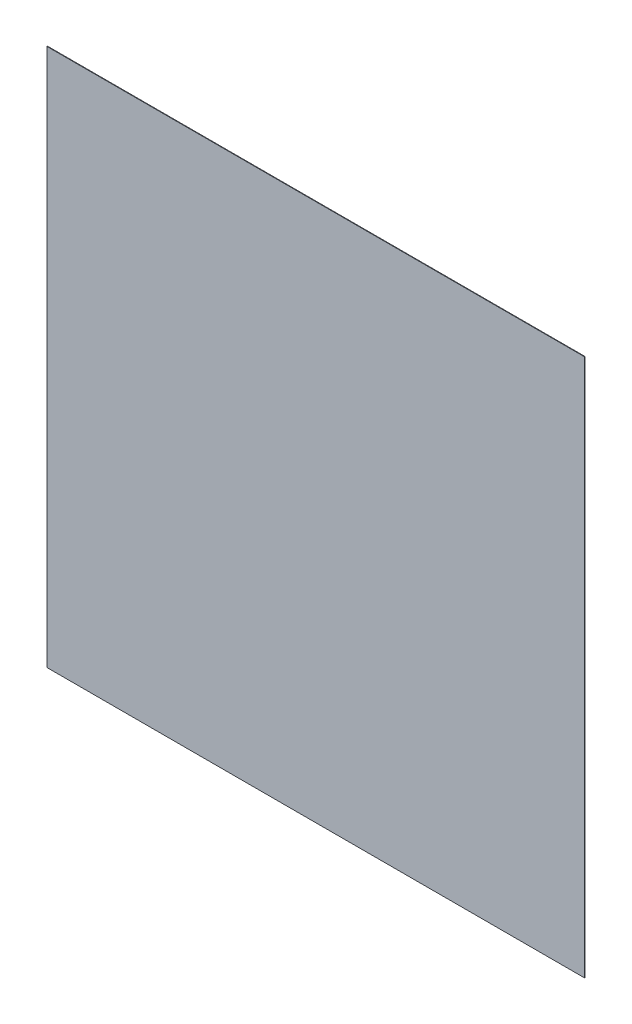
SolidWorks part; units mm, degrees
ref_plane "Front Plane" through (0, 0, 0) normal (0, 0, 1) x (1, 0, 0)
ref_plane "Top Plane" through (0, 0, 0) normal (0, 1, 0) x (1, 0, 0)
ref_plane "Right Plane" through (0, 0, 0) normal (1, 0, 0) x (0, 0, -1)
sketch "Sketch1" plane through (0, 0, 0) normal (0, 0, 1) x (1, 0, 0)
  line L1 (-307.5269, 151.3924) -> (692.4731, 151.3924)
  line L2 (-307.5269, 151.3924) -> (-307.5269, -848.6076)
  line L3 (-307.5269, -848.6076) -> (692.4731, -848.6076)
  line L4 (692.4731, 151.3924) -> (692.4731, -848.6076)
  dimension "D1" = 1000
  dimension "D2" = 1000
extrude "Boss-Extrude1" add sketch "Sketch1" along normal blind 1
